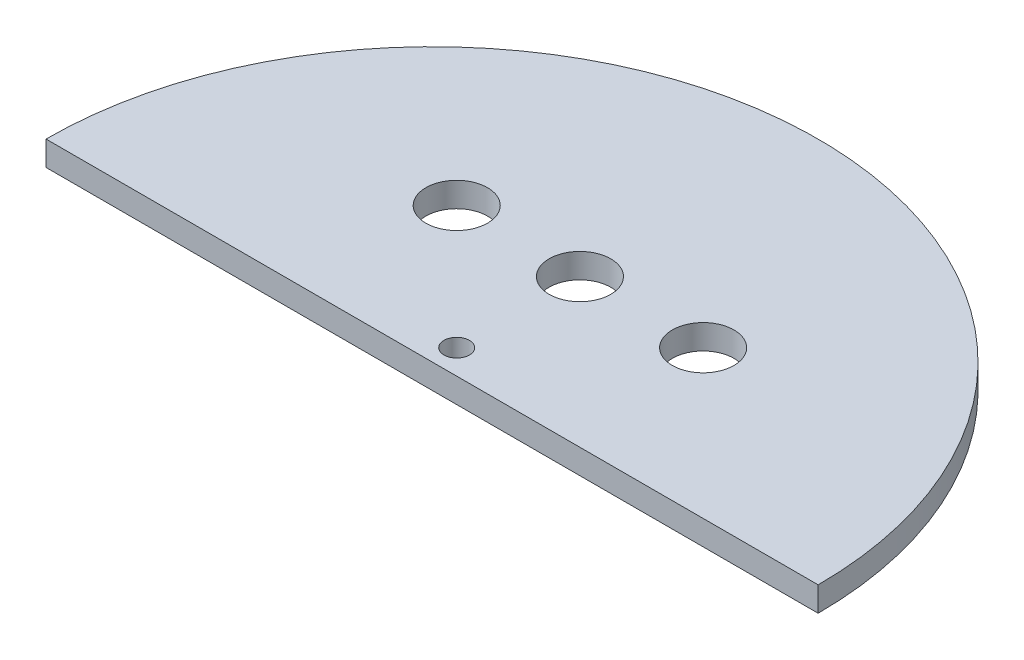
SolidWorks part; units mm, degrees
ref_plane "Front Plane" through (0, 0, 0) normal (0, 0, 1) x (1, 0, 0)
ref_plane "Top Plane" through (0, 0, 0) normal (0, 1, 0) x (1, 0, 0)
ref_plane "Right Plane" through (0, 0, 0) normal (1, 0, 0) x (0, 0, -1)
sketch "Sketch1" plane through (0, 0, 0) normal (0, 1, 0) x (1, 0, 0)
  line L0 (0, 0) -> (94, 0)
  arc A0 (0, 0) -> (94, 0) centre (47, 0) cw
  circle A1 centre (47, 3) radius 1.55
  point P4 (47, 0)
  point P5 (47, 47)
  dimension "D3" = 3.1
  dimension "D1" = 94
  dimension "D2" = 47
  dimension "D4" = 47
  dimension "D5" = 3
extrude "Boss-Extrude1" add sketch "Sketch1" along normal blind 3
sketch "Sketch2" plane through (0, 3, 0) normal (0, 1, 0) x (1, 0, 0)
  line L0 (0, 0) -> (94, 0) construction
  circle A0 centre (47, 18) radius 3.75
  circle A1 centre (32, 18) radius 3.75
  circle A2 centre (62, 18) radius 3.75
  point P9 (47, 0)
  dimension "D1" = 7.5
  dimension "D2" = 7.5
  dimension "D3" = 7.5
  dimension "D4" = 15
  dimension "D5" = 15
  dimension "D6" = 18
extrude "Cut-Extrude1" cut sketch "Sketch2" against normal blind 3
